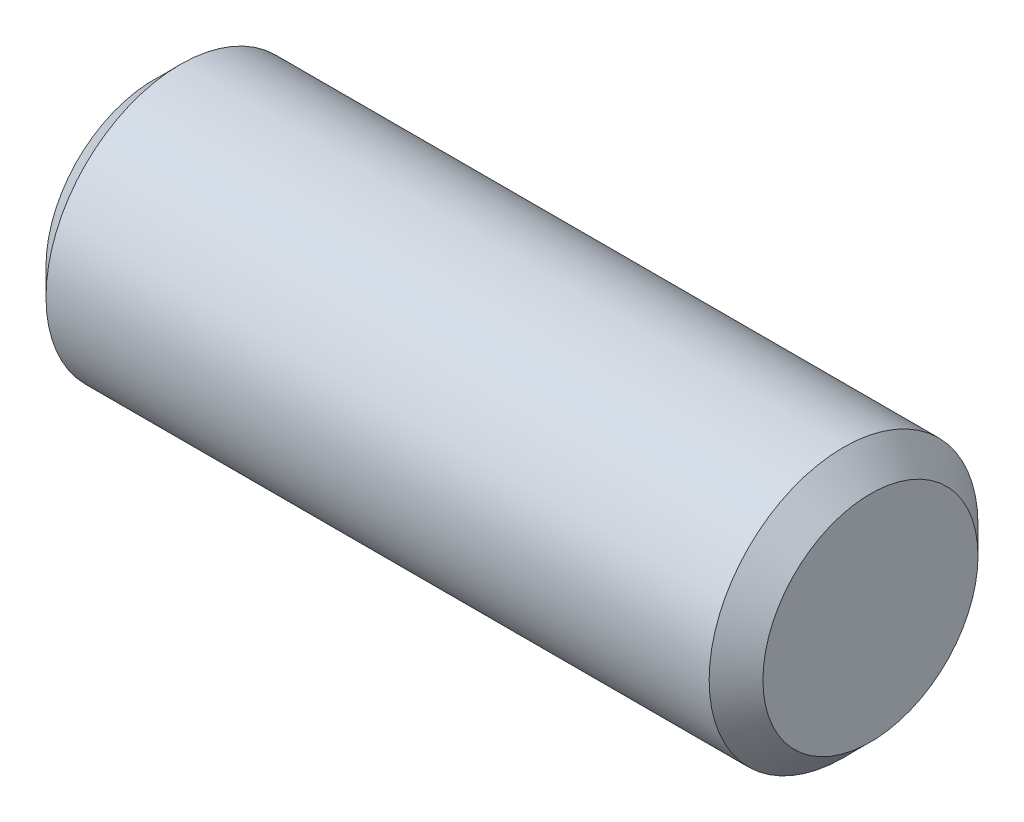
SolidWorks part; units mm, degrees
ref_plane "Front" through (0, 0, 0) normal (0, 0, 1) x (1, 0, 0)
ref_plane "Top" through (0, 0, 0) normal (0, 1, 0) x (1, 0, 0)
ref_plane "Right" through (0, 0, 0) normal (1, 0, 0) x (0, 0, -1)
sketch "Sketch1" plane through (0, 0, 0) normal (0, 0, 1) x (1, 0, 0)
  line L0 (-6.35, 0) -> (6.35, 0) construction
  line L1 (6.35, 2.3813) -> (6.35, -2.3813) construction
  line L2 (-6.35, 2.3813) -> (-6.35, -2.3813) construction
  dimension "Length" = 12.7
  dimension "Diameter" = 4.7625
sketch "Sketch2" plane through (0, 0, 0) normal (1, 0, 0) x (0, 0, -1)
  circle A0 centre (0, 0) radius 2.3813
extrude "Extrude1" add sketch "Sketch2" against normal up to vertex (6.35 mm away) and the other way up to vertex (6.35 mm away) up to point (-6.35, 2.3813, 0) other way up to point (6.35, 2.3813, 0)
chamfer "Chamfer1" distance 0.4763 angle 45 2 edges at (6.35, 0, -2.3813) (-6.35, 0, -2.3813)
equation "\"D1@Chamfer1\" = \"Diameter@Sketch1\"*.1"
